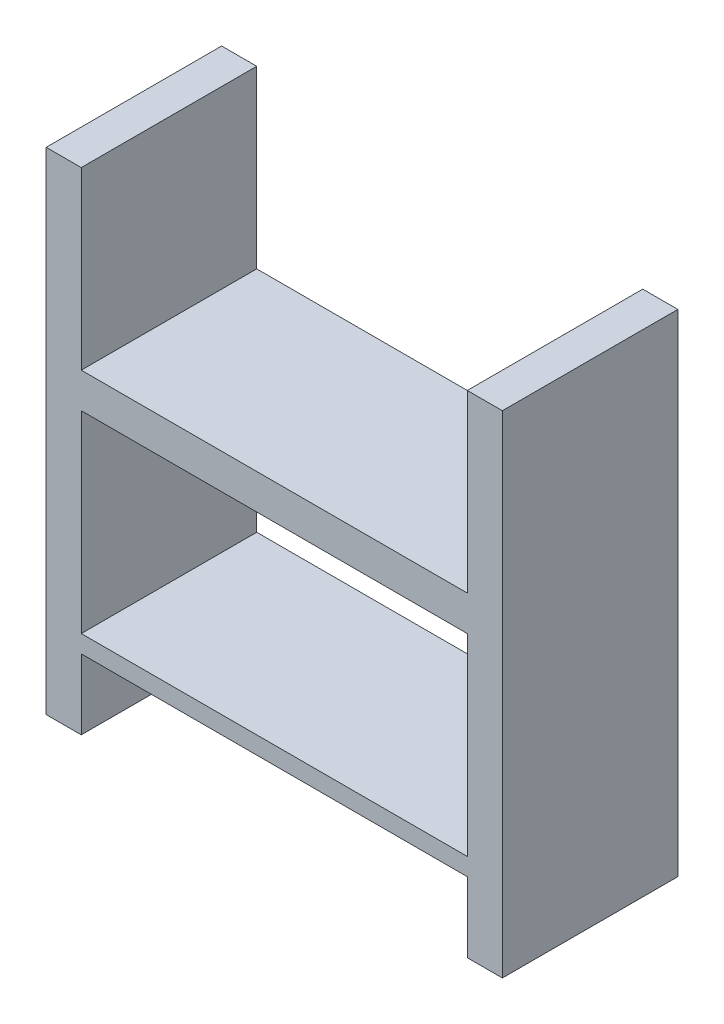
SolidWorks part; units mm, degrees
ref_plane "Front Plane" through (0, 0, 0) normal (0, 0, 1) x (1, 0, 0)
ref_plane "Top Plane" through (0, 0, 0) normal (0, 1, 0) x (1, 0, 0)
ref_plane "Right Plane" through (0, 0, 0) normal (1, 0, 0) x (0, 0, -1)
sketch "Sketch2" plane through (0, 0, 0) normal (0, 0, 1) x (1, 0, 0)
  line L0 (-55, -20) -> (-55, 35)
  line L1 (-55, 45) -> (55, 45)
  line L2 (-65, 45) -> (-65, -45)
  line L3 (-65, -45) -> (-55, -45)
  line L4 (65, 45) -> (65, -45)
  line L5 (-65, 45) -> (65, -45) construction
  line L6 (-65, -45) -> (50.5556, 35) construction
  line L8 (-55, -45) -> (-55, -25)
  line L9 (-55, -25) -> (55, -25)
  line L10 (55, -45) -> (55, -25)
  line L11 (-55, -20) -> (55, -20)
  line L15 (55, -20) -> (55, 35)
  line L16 (55, 95) -> (65, 95)
  line L17 (-55, 45) -> (55, 45)
  line L18 (-65, 45) -> (-65, 95)
  line L19 (-65, 95) -> (-55, 95)
  line L20 (65, 45) -> (65, 95)
  line L21 (-55, 45) -> (-55, 95)
  line L23 (55, 45) -> (55, 95)
  line L24 (-55, 35) -> (55, 35)
  line L25 (55, -45) -> (65, -45)
  point P0 (0, 0)
  dimension "D1" = 130
  dimension "D2" = 90
  dimension "D3" = 20
  dimension "D4" = 10
  dimension "D5" = 10
  dimension "D6" = 5
  dimension "D8" = 50
extrude "Boss-Extrude1" add sketch "Sketch2" along normal blind 50 contours L10 L25 L4 L20 L16 L23 L1 L21 L19 L18 L2 L3 L8 L9 L0 L24 L15 L11
